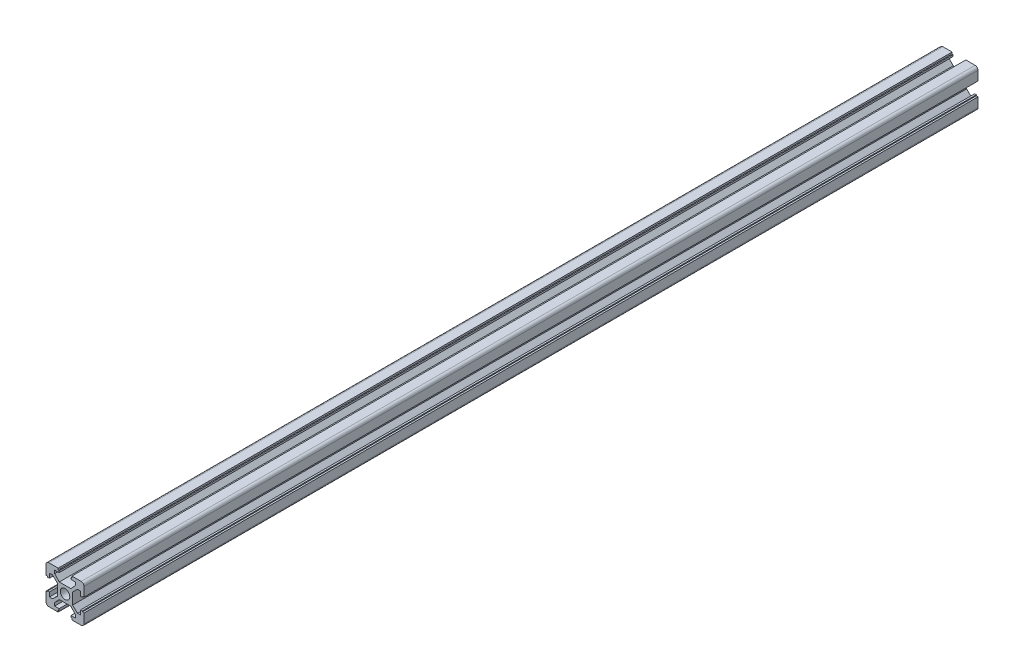
SolidWorks part; units mm, degrees
ref_plane "前视基准面" through (0, 0, 0) normal (0, 0, 1) x (1, 0, 0)
ref_plane "上视基准面" through (0, 0, 0) normal (0, 1, 0) x (1, 0, 0)
ref_plane "右视基准面" through (0, 0, 0) normal (1, 0, 0) x (0, 0, -1)
sketch "草图1" plane through (0, 0, 0) normal (0, 0, 1) x (1, 0, 0)
  line L0 (0, 0) -> (0, 12.7114) construction
  line L1 (0, 0) -> (12.7618, 0) construction
  line L2 (-3.0125, 4) -> (3.0125, 4)
  line L3 (0, 0) -> (12.1278, 12.1278) construction
  line L4 (3.0125, 4) -> (5.45, 6.5847)
  line L5 (5.45, 6.5847) -> (5.45, 8.2)
  line L6 (5.45, 8.2) -> (3.1, 8.2)
  line L7 (3.1, 8.2) -> (3.1, 9.1)
  line L8 (3.1, 9.1) -> (3.6, 9.1)
  line L9 (3.6, 9.1) -> (3.6, 10)
  line L10 (3.6, 10) -> (10, 10)
  line L11 (10, 3.6) -> (10, 10)
  line L12 (9.1, 3.6) -> (10, 3.6)
  line L13 (9.1, 3.1) -> (9.1, 3.6)
  line L14 (8.2, 3.1) -> (9.1, 3.1)
  line L15 (8.2, 5.45) -> (8.2, 3.1)
  line L16 (6.5847, 5.45) -> (8.2, 5.45)
  line L17 (4, 3.0125) -> (6.5847, 5.45)
  line L18 (4, -3.0125) -> (4, 3.0125)
  line L19 (4, -3.0125) -> (6.5847, -5.45)
  line L20 (6.5847, -5.45) -> (8.2, -5.45)
  line L21 (8.2, -5.45) -> (8.2, -3.1)
  line L22 (8.2, -3.1) -> (9.1, -3.1)
  line L23 (9.1, -3.1) -> (9.1, -3.6)
  line L24 (9.1, -3.6) -> (10, -3.6)
  line L25 (10, -3.6) -> (10, -10)
  line L26 (3.6, -10) -> (10, -10)
  line L27 (3.6, -9.1) -> (3.6, -10)
  line L28 (3.1, -9.1) -> (3.6, -9.1)
  line L29 (3.1, -8.2) -> (3.1, -9.1)
  line L30 (5.45, -8.2) -> (3.1, -8.2)
  line L31 (5.45, -6.5847) -> (5.45, -8.2)
  line L32 (3.0125, -4) -> (5.45, -6.5847)
  line L33 (-3.0125, -4) -> (3.0125, -4)
  line L34 (-3.0125, -4) -> (-5.45, -6.5847)
  line L35 (-5.45, -6.5847) -> (-5.45, -8.2)
  line L36 (-5.45, -8.2) -> (-3.1, -8.2)
  line L37 (-3.1, -8.2) -> (-3.1, -9.1)
  line L38 (-3.1, -9.1) -> (-3.6, -9.1)
  line L39 (-3.6, -9.1) -> (-3.6, -10)
  line L40 (-3.6, -10) -> (-10, -10)
  line L41 (-10, -3.6) -> (-10, -10)
  line L42 (-9.1, -3.6) -> (-10, -3.6)
  line L43 (-9.1, -3.1) -> (-9.1, -3.6)
  line L44 (-8.2, -3.1) -> (-9.1, -3.1)
  line L45 (-8.2, -5.45) -> (-8.2, -3.1)
  line L46 (-6.5847, -5.45) -> (-8.2, -5.45)
  line L47 (-4, -3.0125) -> (-6.5847, -5.45)
  line L48 (-4, -3.0125) -> (-4, 3.0125)
  line L49 (-4, 3.0125) -> (-6.5847, 5.45)
  line L50 (-6.5847, 5.45) -> (-8.2, 5.45)
  line L51 (-8.2, 5.45) -> (-8.2, 3.1)
  line L52 (-8.2, 3.1) -> (-9.1, 3.1)
  line L53 (-9.1, 3.1) -> (-9.1, 3.6)
  line L54 (-9.1, 3.6) -> (-10, 3.6)
  line L55 (-10, 3.6) -> (-10, 10)
  line L56 (-3.6, 10) -> (-10, 10)
  line L57 (-3.6, 9.1) -> (-3.6, 10)
  line L58 (-3.1, 9.1) -> (-3.6, 9.1)
  line L59 (-3.1, 8.2) -> (-3.1, 9.1)
  line L60 (-5.45, 8.2) -> (-3.1, 8.2)
  line L61 (-5.45, 6.5847) -> (-5.45, 8.2)
  line L62 (-3.0125, 4) -> (-5.45, 6.5847)
  circle A0 centre (0, 0) radius 2.5
  point P4 (5.2924, 4.2313)
  point P5 (-4, 0)
  point P24 (4, 0)
  point P40 (0, -4)
  point P69 (0, 4)
  dimension "D9" = 5
  dimension "D1" = 4
  dimension "D3" = 5.45
  dimension "D4" = 8.2
  dimension "D5" = 3.1
  dimension "D6" = 3.6
  dimension "D7" = 0.9
  dimension "D8" = 1.8
  dimension "D10" = 1.5
extrude "凸台-拉伸1" add sketch "草图1" along normal blind 470
fillet "圆角1" radius 1.5 4 edges at (10, -10, 235) (-10, -10, 235) (-10, 10, 235) (10, 10, 235)
